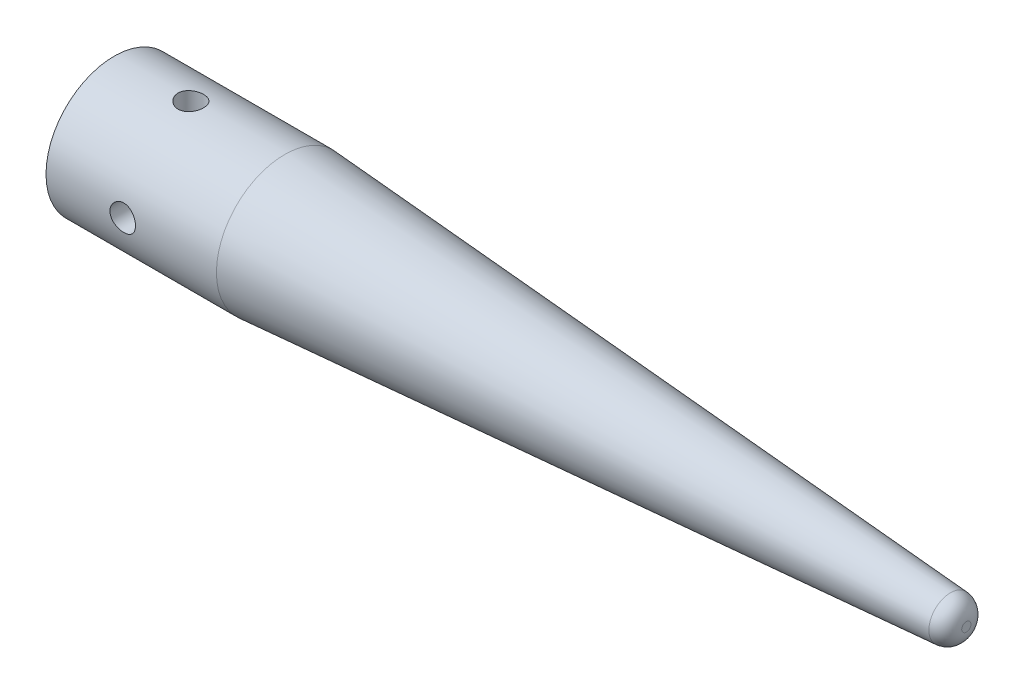
SolidWorks part; units mm, degrees
ref_plane "Plan de face" through (0, 0, 0) normal (0, 0, 1) x (1, 0, 0)
ref_plane "Plan de dessus" through (0, 0, 0) normal (0, 1, 0) x (1, 0, 0)
ref_plane "Plan de droite" through (0, 0, 0) normal (1, 0, 0) x (0, 0, -1)
sketch "Esquisse1" plane through (0, 0, 0) normal (0, 0, 1) x (1, 0, 0)
  line L0 (0, 0) -> (120.7576, 0) construction
  line L1 (7.9, 0) -> (0, 7.9)
  line L4 (0, 8) -> (20, 8)
  line L5 (20, 8) -> (98.1395, 2.536)
  line L6 (100, 0.5408) -> (100, 0)
  line L11 (0, 8) -> (0, 7.9)
  line L13 (7.9, 0) -> (100, 0)
  arc A0 (98.1395, 2.536) -> (100, 0.5408) centre (98, 0.5408) cw
revolve "Révolution1" add sketch "Esquisse1" angle 360 about L0
sketch "Esquisse2" plane through (0, 0, 0) normal (1, 0, 0) x (0, 0, -1)
  line L1 (4, 5) -> (-4, 5)
  line L2 (5, 4) -> (5, -4)
  line L3 (4, -5) -> (-4, -5)
  line L4 (-5, 4) -> (-5, -4)
  line L5 (5, 5) -> (-5, -5) construction
  line L6 (5, -5) -> (-5, 5) construction
  arc A0 (5, -4) -> (4, -5) centre (4, -4) cw
  arc A1 (-4, -5) -> (-5, -4) centre (-4, -4) cw
  arc A2 (-4, 5) -> (-5, 4) centre (-4, 4) ccw
  arc A3 (4, 5) -> (5, 4) centre (4, 4) cw
  point P0 (0, 0)
extrude "Enlèv. mat.-Extru.1" cut sketch "Esquisse2" along a picked direction on the side of the normal blind 15
sketch "Esquisse3" plane through (0, 0, 0) normal (0, 1, 0) x (1, 0, 0)
  line L0 (0, 8) -> (0, -8) construction
  circle A0 centre (9, 0) radius 1.5
  point P2 (0, 0)
extrude "Enlèv. mat.-Extru.2" cut sketch "Esquisse3" against normal through all both and the other way through all
sketch "Esquisse4" plane through (0, 0, 0) normal (0, 0, 1) x (1, 0, 0)
  line L0 (0, 8) -> (0, -8) construction
  circle A0 centre (9, 0) radius 1.5
  point P2 (0, 0)
extrude "Enlèv. mat.-Extru.3" cut sketch "Esquisse4" against normal through all both and the other way through all
equation "\"D2@Esquisse2\"=\"D1@Esquisse2\""
equation "\"D6@Esquisse1\"=\"D5@Esquisse1\" - 0.1"
equation "\"D1@Esquisse4\"=\"D1@Esquisse3\""
